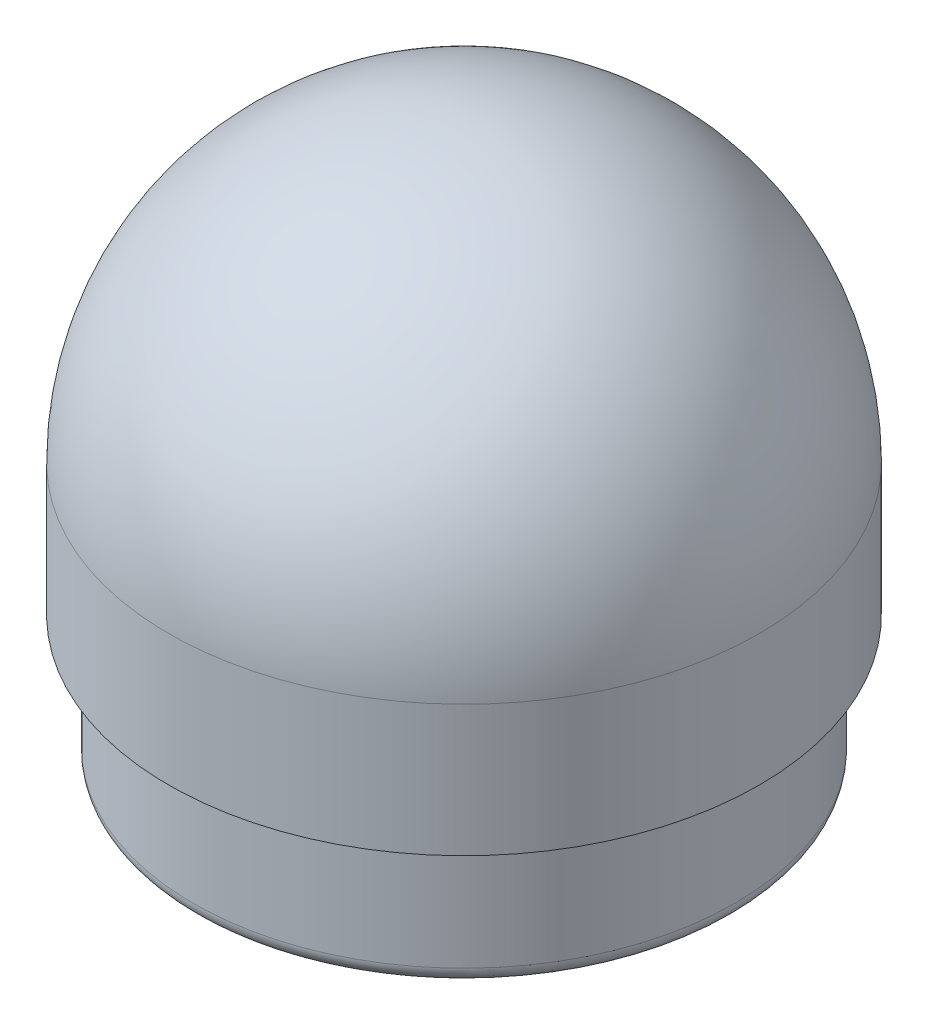
SolidWorks part; units mm, degrees
ref_plane "Front Plane" through (0, 0, 0) normal (0, 0, 1) x (1, 0, 0)
ref_plane "Top Plane" through (0, 0, 0) normal (0, 1, 0) x (1, 0, 0)
ref_plane "Right Plane" through (0, 0, 0) normal (1, 0, 0) x (0, 0, -1)
sketch "Sketch2" plane through (0, 0, 0) normal (0, 0, 1) x (1, 0, 0)
  line L0 (44.45, 0) -> (49.2125, 0)
  line L1 (52.3875, 3.175) -> (52.3875, 25.4)
  line L2 (52.3875, 25.4) -> (57.15, 25.4)
  line L3 (57.15, 25.4) -> (57.15, 50.8)
  line L5 (44.45, 50.8) -> (44.45, 0)
  line L6 (0, 107.95) -> (0, 95.25)
  arc A0 (49.2125, 0) -> (52.3875, 3.175) centre (49.2125, 3.175) ccw
  arc A1 (57.15, 50.8) -> (0, 107.95) centre (0, 50.8) ccw
  arc A2 (44.45, 50.8) -> (0, 95.25) centre (0, 50.8) ccw
  dimension "D3" = 3.175
  dimension "D1" = 57.15
  dimension "D2" = 44.45
  dimension "D4" = 25.4
  dimension "D5" = 0
revolve "Revolve1" add sketch "Sketch2" angle 360 about L6
